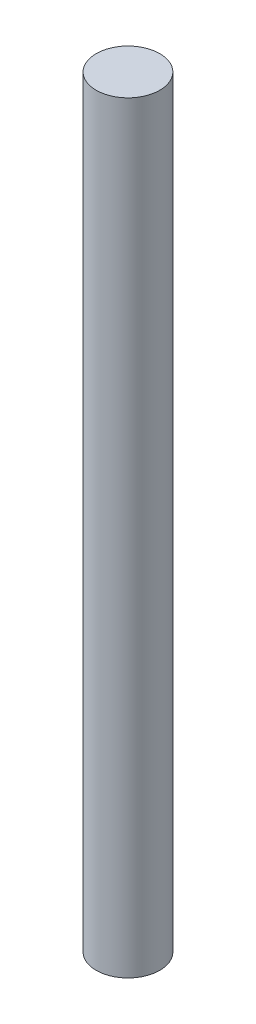
SolidWorks part; units mm, degrees
material "AISI 1045 Aço, trefilado"
ref_plane "Plano frontal" through (0, 0, 0) normal (0, 0, 1) x (1, 0, 0)
ref_plane "Plano superior" through (0, 0, 0) normal (0, 1, 0) x (1, 0, 0)
ref_plane "Plano direito" through (0, 0, 0) normal (1, 0, 0) x (0, 0, -1)
sketch "Esboço1" plane through (0, 0, 0) normal (0, 1, 0) x (1, 0, 0)
  circle A0 centre (0, 0) radius 5
  dimension "D1" = 10
extrude "Ressalto-extrusão1" add sketch "Esboço1" along normal blind 120
